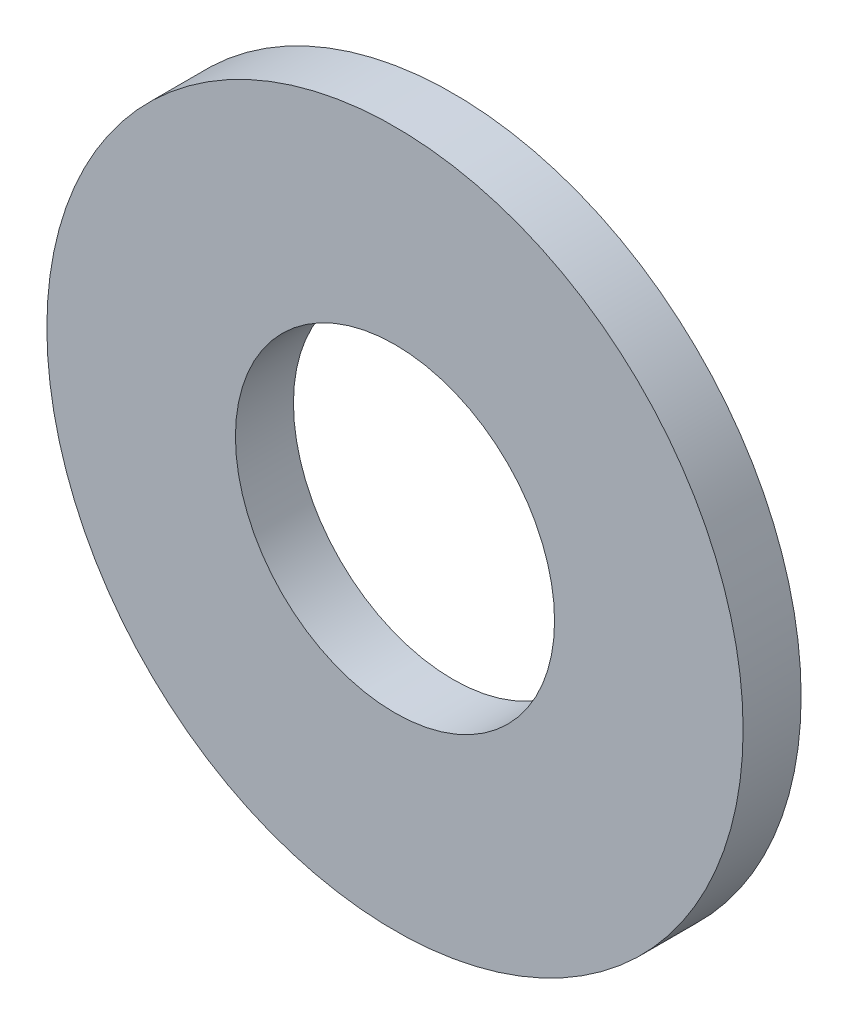
SolidWorks part; units mm, degrees
ref_plane "Front" through (0, 0, 0) normal (0, 0, 1) x (1, 0, 0)
ref_plane "Top" through (0, 0, 0) normal (0, 1, 0) x (1, 0, 0)
ref_plane "Right" through (0, 0, 0) normal (1, 0, 0) x (0, 0, -1)
sketch "Sketch1" plane through (0, 0, 0) normal (0, 0, 1) x (1, 0, 0)
  circle A0 centre (0, 0) radius 6
  circle A1 centre (0, 0) radius 2.75
  dimension "D1" = 12
  dimension "D2" = 5.5
extrude "Boss-Extrude1" add sketch "Sketch1" along normal blind 1
